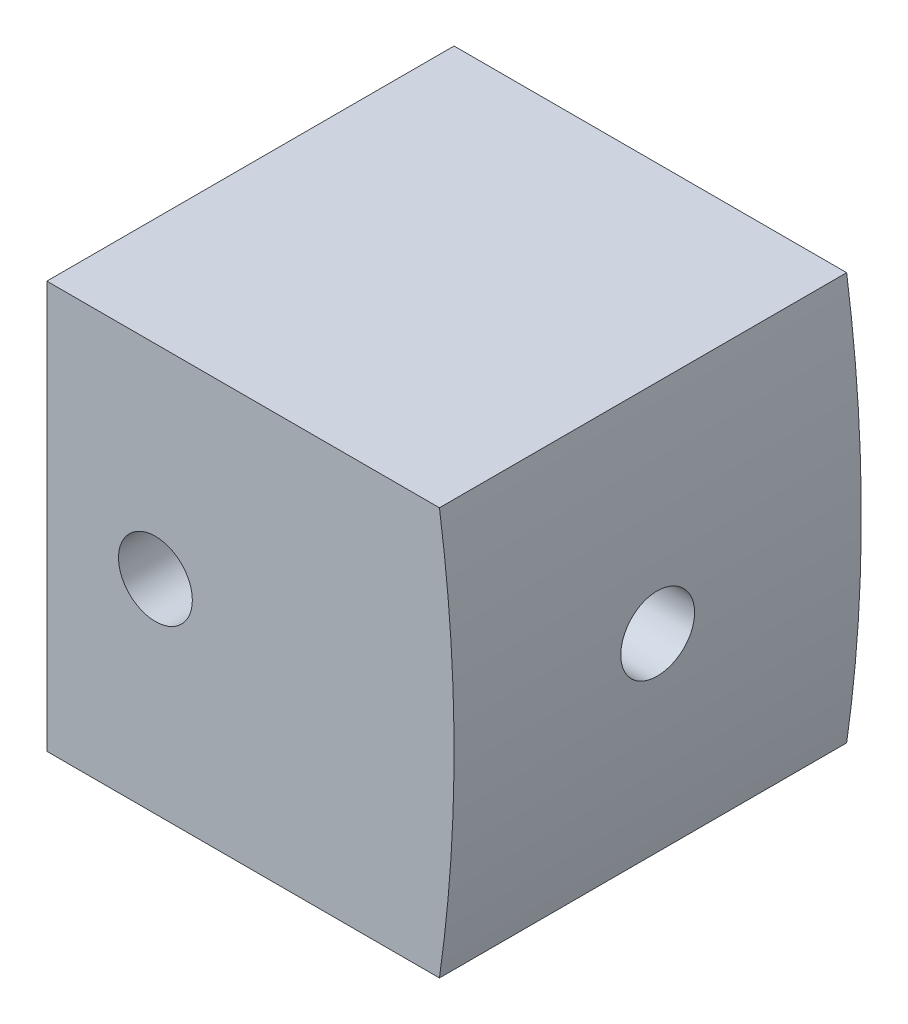
SolidWorks part; units mm, degrees
ref_plane "Front Plane" through (0, 0, 0) normal (0, 0, 1) x (1, 0, 0)
ref_plane "Top Plane" through (0, 0, 0) normal (0, 1, 0) x (1, 0, 0)
ref_plane "Right Plane" through (0, 0, 0) normal (1, 0, 0) x (0, 0, -1)
sketch "Sketch1" plane through (0, 0, 0) normal (0, 0, 1) x (1, 0, 0)
  line L1 (-9.525, -9.525) -> (9.525, -9.525)
  line L2 (-9.525, -9.525) -> (-9.525, 9.525)
  line L3 (-9.525, 9.525) -> (9.525, 9.525)
  line L4 (9.525, -9.525) -> (9.525, 9.525)
  line L5 (-9.525, -9.525) -> (9.525, 9.525) construction
  line L6 (-9.525, 9.525) -> (9.525, -9.525) construction
  point P0 (0, 0)
extrude "Extrude1" add sketch "Sketch1" along normal blind 19.05
sketch "Sketch3" plane through (-9.525, 0, 0) normal (-1, 0, 0) x (0, 0, 1)
  line L0 (9.525, -9.525) -> (9.525, 9.525) construction
  line L1 (19.05, -9.525) -> (0, -9.525) construction
  line L2 (19.05, 9.525) -> (0, 9.525) construction
hole_wizard "#29 (0.136) Diameter Hole1" positions "Sketch6" profile "Sketch5" hole size "#29" standard "Ansi Inch" end condition through all
sketch "Sketch6" plane through (-9.525, 0, 0) normal (-1, 0, 0) x (0, 0, 1)
  line L0 (9.525, -9.525) -> (9.525, 9.525) construction
  point P1 (9.525, 0)
sketch "Sketch5" plane through (-9.525, 0, 9.525) normal (0, 1, 0) x (0, 0, 1)
  line L0 (0, 0) -> (0, 19.05)
  line L1 (0, 19.05) -> (1.7272, 19.05)
  line L2 (1.7272, 19.05) -> (1.7272, 0)
  line L5 (1.7272, 0) -> (0, 0)
  line L11 (0, -6.35) -> (0, 107.95) construction
  dimension "Thru Hole Dia." = 3.4544
  dimension "Thru Hole Depth" = 19.05
sketch "Sketch7" plane through (0, 0, 19.05) normal (0, 0, 1) x (1, 0, 0)
  line L0 (9.525, 0) -> (-57.15, 0) construction
  line L1 (9.525, -9.525) -> (9.525, 9.525) construction
  line L2 (9.525, 9.525) -> (-9.525, 9.525) construction
  line L3 (-9.525, -9.525) -> (9.525, -9.525) construction
  arc A0 (9.525, 0) -> (8.8411, 9.525) centre (-57.15, 0) ccw
  arc A1 (9.525, 0) -> (8.8411, -9.525) centre (-57.15, 0) cw
extrude "Extrude2" cut sketch "Sketch7" against normal through all and the other way through all
sketch "Sketch12" plane through (0, 0, 19.05) normal (0, 0, 1) x (1, 0, 0)
  line L0 (-9.525, 0) -> (-4.445, 0) construction
  line L1 (-9.525, 9.525) -> (-9.525, -9.525) construction
hole_wizard "#29 (0.136) Diameter Hole3" positions "3DSketch4" profile "Sketch14" hole size "#29" standard "Ansi Inch" end condition through all
sketch3d "3DSketch4"
  point P0 (-4.445, 0, 19.05)
sketch "Sketch14" plane through (-4.445, 0, 19.05) normal (1, 0, 0) x (0, -1, 0)
  line L0 (0, 0) -> (0, 19.05)
  line L1 (0, 19.05) -> (1.7272, 19.05)
  line L2 (1.7272, 19.05) -> (1.7272, 0)
  line L5 (1.7272, 0) -> (0, 0)
  line L11 (0, -6.35) -> (0, 107.95) construction
  dimension "Thru Hole Dia." = 3.4544
  dimension "Thru Hole Depth" = 19.05
